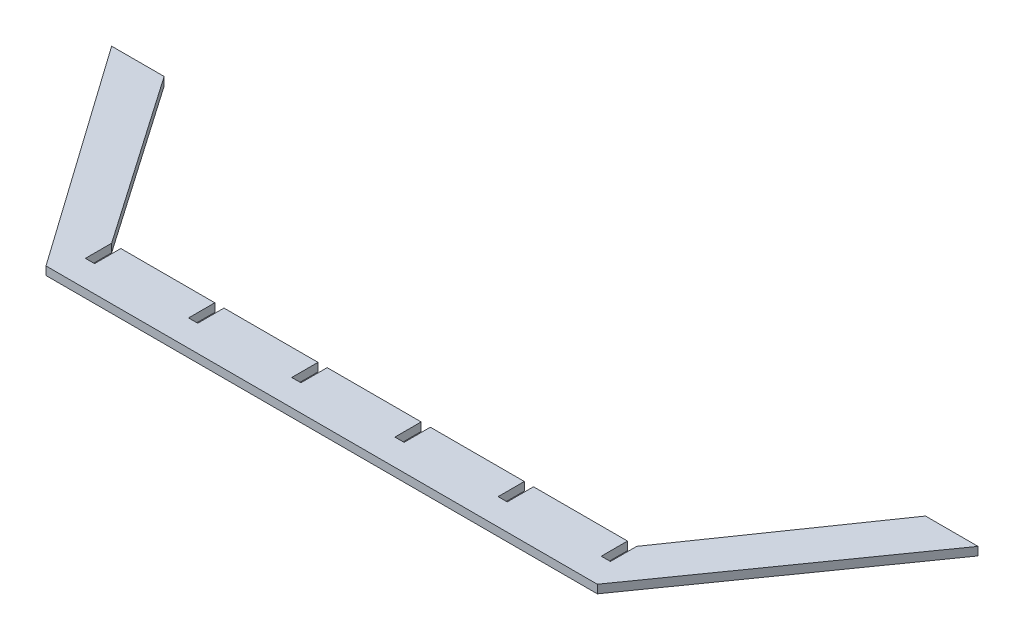
SolidWorks part; units mm, degrees
ref_plane "Front Plane" through (0, 0, 0) normal (0, 0, 1) x (1, 0, 0)
ref_plane "Top Plane" through (0, 0, 0) normal (0, 1, 0) x (1, 0, 0)
ref_plane "Right Plane" through (0, 0, 0) normal (1, 0, 0) x (0, 0, -1)
sketch "Sketch2" plane through (0, 0, 0) normal (0, 1, 0) x (1, 0, 0)
  line L0 (0, 0) -> (-5, 0)
  line L1 (0, 0) -> (200, 0)
  line L3 (0, 20) -> (200, 20)
  line L5 (-5, 0) -> (-65, 85)
  line L6 (-65, 85) -> (-45, 85)
  line L7 (-45, 85) -> (0, 20)
  line L8 (200, 0) -> (205, 0)
  line L9 (205, 0) -> (265, 85)
  line L10 (200, 20) -> (245, 85)
  line L11 (245, 85) -> (265, 85)
  dimension "D1" = 200
  dimension "D2" = 20
  dimension "D3" = 5
  dimension "D4" = 60
  dimension "D5" = 85
  dimension "D6" = 20
  dimension "D7" = 5
  dimension "D8" = 60
  dimension "D9" = 85
  dimension "D10" = 20
extrude "Boss-Extrude1" add sketch "Sketch2" along normal blind 3.175
sketch "Sketch3" plane through (0, 3.175, 0) normal (0, 1, 0) x (1, 0, 0)
  line L1 (39.3, 20) -> (39.3, 10)
  line L2 (0, 20) -> (3.5, 20)
  line L3 (0, 20) -> (0, 10)
  line L4 (0, 10) -> (3.5, 10)
  line L5 (3.5, 20) -> (3.5, 10)
  line L6 (39.3, 20) -> (42.8, 20)
  line L7 (42.8, 20) -> (42.8, 10)
  line L8 (39.3, 10) -> (42.8, 10)
  line L9 (78.6, 20) -> (78.6, 10)
  line L10 (78.6, 20) -> (82.1, 20)
  line L11 (82.1, 20) -> (82.1, 10)
  line L12 (78.6, 10) -> (82.1, 10)
  line L13 (117.9, 20) -> (117.9, 10)
  line L14 (117.9, 20) -> (121.4, 20)
  line L15 (121.4, 20) -> (121.4, 10)
  line L16 (117.9, 10) -> (121.4, 10)
  line L17 (157.2, 20) -> (157.2, 10)
  line L18 (157.2, 20) -> (160.7, 20)
  line L19 (160.7, 20) -> (160.7, 10)
  line L20 (157.2, 10) -> (160.7, 10)
  line L21 (196.5, 20) -> (196.5, 10)
  line L22 (196.5, 20) -> (200, 20)
  line L23 (200, 20) -> (200, 10)
  line L24 (196.5, 10) -> (200, 10)
  line L25 (0, 20) -> (39.3, 20) construction
  dimension "D1" = 10
  dimension "D2" = 3.5
  dimension "D4" = 39.3
  dimension "D3" = 6
extrude "Cut-Extrude1" cut sketch "Sketch3" against normal through all
